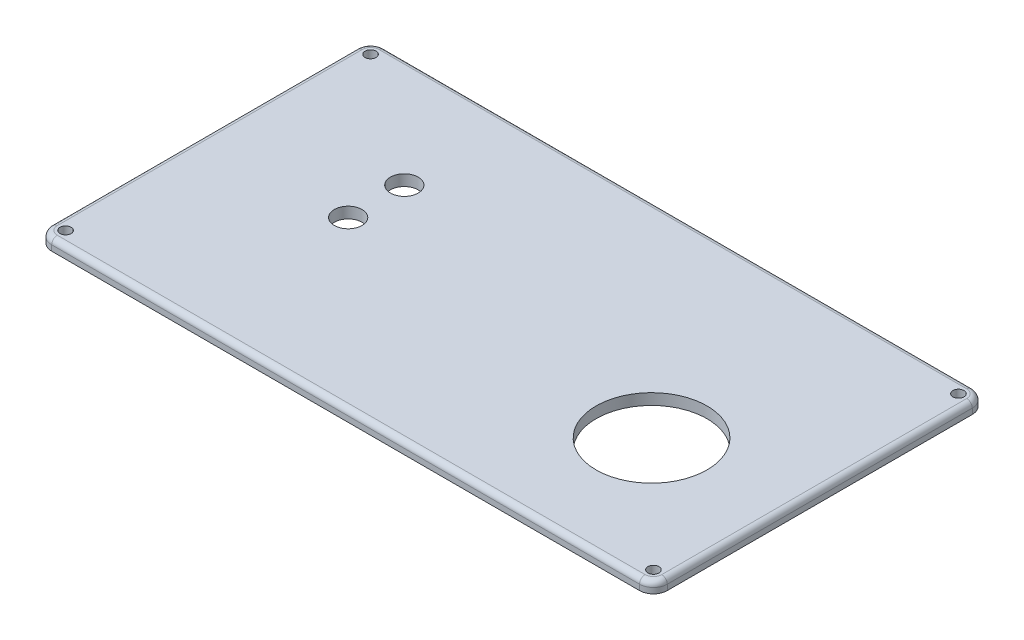
SolidWorks part; units mm, degrees
ref_plane "Front Plane" through (0, 0, 0) normal (0, 0, 1) x (1, 0, 0)
ref_plane "Top Plane" through (0, 0, 0) normal (0, 1, 0) x (1, 0, 0)
ref_plane "Right Plane" through (0, 0, 0) normal (1, 0, 0) x (0, 0, -1)
sketch "Sketch1" plane through (0, 0, 0) normal (0, 1, 0) x (1, 0, 0)
  line L1 (0, 0) -> (111, 0)
  line L2 (0, 0) -> (0, 60)
  line L3 (0, 60) -> (111, 60)
  line L4 (111, 0) -> (111, 60)
  dimension "D1" = 111
  dimension "D2" = 60
extrude "Boss-Extrude1" add sketch "Sketch1" along normal blind 2
sketch "Sketch2" plane through (0, 2, 0) normal (0, 1, 0) x (1, 0, 0)
  line L0 (0, 60) -> (0, 0) construction
  line L6 (111, 0) -> (111, 60) construction
  line L7 (111, 60) -> (0, 60) construction
  line L8 (0, 0) -> (111, 0) construction
  circle A2 centre (87.7359, 22.9285) radius 10
  circle A3 centre (2.5, 57.5) radius 1
  circle A4 centre (108.5, 57.5) radius 1
  circle A5 centre (108.5, 2.5) radius 1
  circle A6 centre (2.5, 2.5) radius 1
  circle A7 centre (25.9625, 30) radius 2.5
  circle A8 centre (25.9625, 40.1182) radius 2.5
  point P28 (0, 0)
  point P29 (0, 0)
  dimension "D9" = 2
  dimension "D10" = 2
  dimension "D15" = 2
  dimension "D16" = 2
  dimension "D2" = 5
  dimension "D3" = 5
  dimension "D4" = 20
  dimension "D7" = 2.5
  dimension "D8" = 2.5
  dimension "D11" = 2.5
  dimension "D12" = 2.5
  dimension "D13" = 2.5
  dimension "D14" = 2.5
  dimension "D17" = 2.5
  dimension "D18" = 2.5
extrude "Cut-Extrude1" cut sketch "Sketch2" against normal through all
fillet "Fillet1" radius 2.5 4 edges at (0, 1, -60) (0, 1, 0) (111, 1, -60) (111, 1, 0)
fillet "Fillet2" radius 1 8 edges at (55.5, 2, -60) (110.2678, 2, -59.2678) (111, 2, -30) (110.2678, 2, -0.7322) (55.5, 2, 0) (0.7322, 2, -0.7322) (0, 2, -30) (0.7322, 2, -59.2678)
